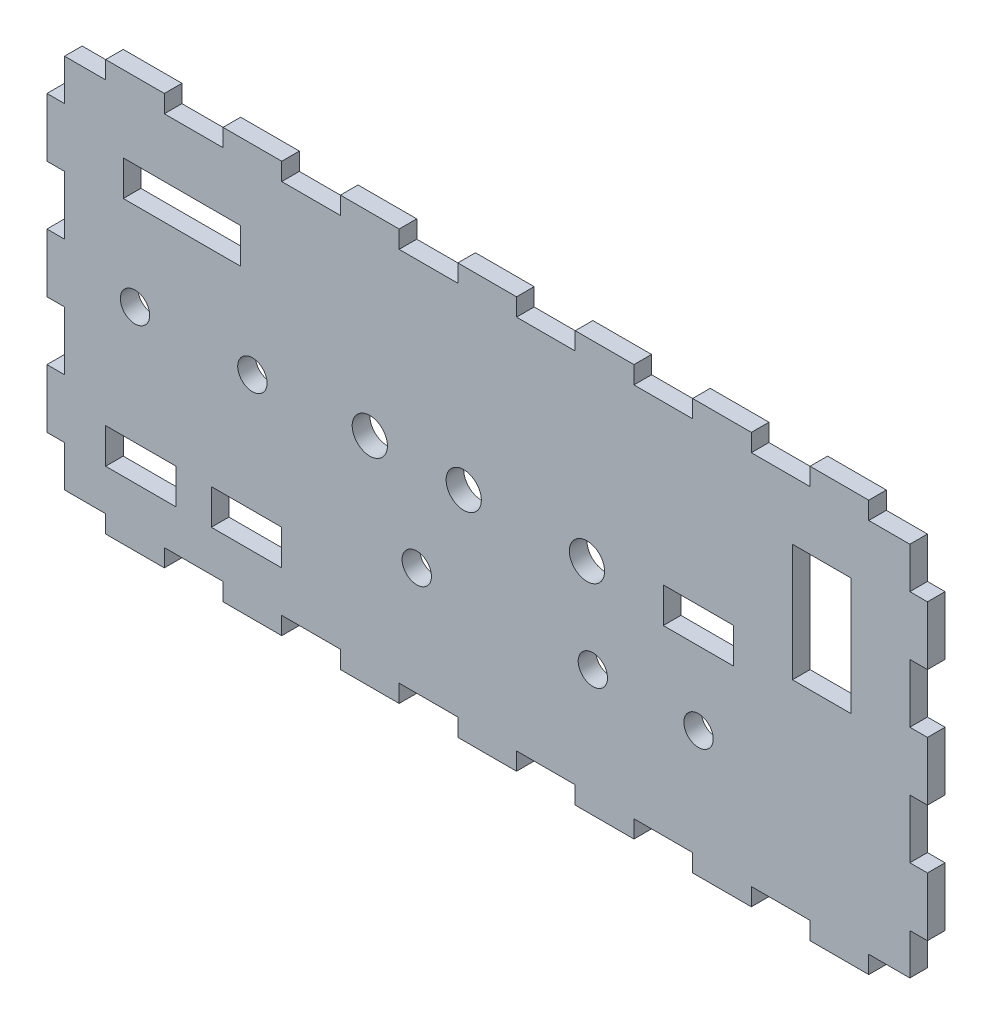
SolidWorks part; units mm, degrees
ref_plane "Front Plane" through (0, 0, 0) normal (0, 0, 1) x (1, 0, 0)
ref_plane "Top Plane" through (0, 0, 0) normal (0, 1, 0) x (1, 0, 0)
ref_plane "Right Plane" through (0, 0, 0) normal (1, 0, 0) x (0, 0, -1)
sketch "Sketch1" plane through (0, 0, 0) normal (0, 0, 1) x (1, 0, 0)
  line L1 (-75, 35) -> (75, 35)
  line L2 (-75, 35) -> (-75, -35)
  line L3 (-75, -35) -> (75, -35)
  line L4 (75, 35) -> (75, -35)
  line L5 (-75, 35) -> (75, -35) construction
  line L6 (-75, -35) -> (75, 35) construction
  point P0 (0, 0)
  dimension "D1" = 150
  dimension "D2" = 70
extrude "Boss-Extrude1" add sketch "Sketch1" along normal blind 3
sketch "Sketch2" plane through (0, 0, 3) normal (0, 0, 1) x (1, 0, 0)
  line L1 (-75, 35) -> (-65, 35)
  line L2 (-75, 35) -> (-75, 32)
  line L3 (-75, 32) -> (-65, 32)
  line L4 (-65, 35) -> (-65, 32)
  dimension "D1" = 3
  dimension "D2" = 10
extrude "Cut-Extrude1" cut sketch "Sketch2" against normal blind 3
pattern_linear "LPattern3" count 8 spacing 20 along (1, 0, 0) of "Cut-Extrude1"
mirror "Mirror1" about plane through (0, 0, 0) normal (0, 1, 0) of "LPattern3", "Cut-Extrude1"
sketch "Sketch3" plane through (0, 0, 3) normal (0, 0, 1) x (1, 0, 0)
  line L0 (-75, 32) -> (-75, -32) construction
  line L1 (-75, 25) -> (-72, 25)
  line L2 (-75, 25) -> (-75, 35)
  line L3 (-75, 35) -> (-72, 35)
  line L4 (-72, 25) -> (-72, 35)
  line L5 (-55, 35) -> (-65, 35) construction
  dimension "D1" = 10
  dimension "D2" = 3
extrude "Cut-Extrude2" cut sketch "Sketch3" against normal blind 3
pattern_linear "LPattern4" count 4 spacing 20 along (0, -1, 0) of "Cut-Extrude2"
mirror "Mirror2" about plane through (0, 0, 0) normal (1, 0, 0) of "LPattern4", "Cut-Extrude2"
sketch "Sketch4" plane through (0, 0, 3) normal (0, 0, 1) x (1, 0, 0)
  line L0 (-55, 35) -> (-65, 35) construction
  line L1 (-62, 22) -> (-42, 22)
  line L2 (-62, 22) -> (-62, 16)
  line L3 (-62, 16) -> (-42, 16)
  line L4 (-42, 22) -> (-42, 16)
  line L5 (-75, 25) -> (-75, 15) construction
  dimension "D1" = 20
  dimension "D2" = 6
  dimension "D3" = 13
  dimension "D4" = 13
extrude "Cut-Extrude3" cut sketch "Sketch4" against normal blind 3
sketch "Sketch5" plane through (0, 0, 3) normal (0, 0, 1) x (1, 0, 0)
  line L0 (-62, 16) -> (-42, 16) construction
  line L1 (-75, 5) -> (-75, -5) construction
  circle A0 centre (-60, 1) radius 2.5
  circle A1 centre (-40, 1) radius 2.5
  dimension "D1" = 5
  dimension "D2" = 5
  dimension "D3" = 15
  dimension "D4" = 15
  dimension "D5" = 15
  dimension "D6" = 20
extrude "Cut-Extrude5" cut sketch "Sketch5" against normal blind 3
sketch "Sketch6" plane through (0, 0, 3) normal (0, 0, 1) x (1, 0, 0)
  line L0 (-65, -35) -> (-55, -35) construction
  line L1 (-65, -19) -> (-53, -19)
  line L2 (-65, -19) -> (-65, -25)
  line L3 (-65, -25) -> (-53, -25)
  line L4 (-53, -19) -> (-53, -25)
  line L5 (-47, -19) -> (-35, -19)
  line L6 (-47, -19) -> (-47, -25)
  line L7 (-47, -25) -> (-35, -25)
  line L8 (-35, -19) -> (-35, -25)
  line L9 (-75, -15) -> (-75, -25) construction
  line L10 (-45, -35) -> (-35, -35) construction
  dimension "D1" = 12
  dimension "D2" = 6
  dimension "D3" = 12
  dimension "D4" = 6
  dimension "D5" = 6
  dimension "D6" = 10
  dimension "D7" = 10
  dimension "D8" = 10
extrude "Cut-Extrude6" cut sketch "Sketch6" against normal blind 3
sketch "Sketch7" plane through (0, 0, 3) normal (0, 0, 1) x (1, 0, 0)
  line L0 (-15, 35) -> (-25, 35) construction
  line L1 (5, 35) -> (-5, 35) construction
  circle A0 centre (-20, 2) radius 3
  circle A1 centre (-4, 2) radius 3
  circle A2 centre (-40, 1) radius 2.5 construction
  dimension "D1" = 6
  dimension "D2" = 6
  dimension "D3" = 20
  dimension "D4" = 16
  dimension "D5" = 33
  dimension "D6" = 33
extrude "Cut-Extrude7" cut sketch "Sketch7" against normal blind 3
sketch "Sketch8" plane through (0, 0, 3) normal (0, 0, 1) x (1, 0, 0)
  line L0 (-75, -15) -> (-75, -25) construction
  circle A0 centre (-12, -13.5) radius 2.5
  circle A1 centre (-20, 2) radius 3 construction
  dimension "D1" = 5
  dimension "D3" = 15.5
  dimension "D2" = 63
extrude "Cut-Extrude8" cut sketch "Sketch8" against normal blind 3
sketch "Sketch9" plane through (0, 0, 3) normal (0, 0, 1) x (1, 0, 0)
  line L0 (25, 35) -> (15, 35) construction
  circle A0 centre (17, 2) radius 3
  circle A1 centre (-4, 2) radius 3 construction
  dimension "D1" = 6
  dimension "D3" = 21
  dimension "D2" = 33
extrude "Cut-Extrude9" cut sketch "Sketch9" against normal blind 3
sketch "Sketch10" plane through (0, 0, 3) normal (0, 0, 1) x (1, 0, 0)
  line L0 (45, 35) -> (35, 35) construction
  line L1 (30, 5) -> (42, 5)
  line L2 (30, 5) -> (30, -1)
  line L3 (30, -1) -> (42, -1)
  line L4 (42, 5) -> (42, -1)
  circle A0 centre (17, 2) radius 3 construction
  dimension "D1" = 6
  dimension "D2" = 12
  dimension "D3" = 30
  dimension "D4" = 13
extrude "Cut-Extrude10" cut sketch "Sketch10" against normal blind 3
sketch "Sketch11" plane through (0, 0, 3) normal (0, 0, 1) x (1, 0, 0)
  line L0 (25, 35) -> (15, 35) construction
  line L1 (45, 35) -> (35, 35) construction
  circle A0 centre (18, -13.5) radius 2.5
  circle A1 centre (36, -13.5) radius 2.5
  circle A2 centre (-12, -13.5) radius 2.5 construction
  dimension "D1" = 5
  dimension "D2" = 5
  dimension "D3" = 48.5
  dimension "D4" = 48.5
  dimension "D5" = 18
  dimension "D6" = 30
extrude "Cut-Extrude11" cut sketch "Sketch11" against normal blind 3
sketch "Sketch12" plane through (0, 0, 3) normal (0, 0, 1) x (1, 0, 0)
  line L0 (65, 35) -> (55, 35) construction
  line L1 (52, 22) -> (62, 22)
  line L2 (52, 22) -> (52, 2)
  line L3 (52, 2) -> (62, 2)
  line L4 (62, 22) -> (62, 2)
  line L5 (65, 35) -> (55, 35) construction
  line L6 (75, 15) -> (75, 25) construction
  point P4 (60, 35)
  dimension "D1" = 10
  dimension "D2" = 20
  dimension "D3" = 13
  dimension "D4" = 13
extrude "Cut-Extrude12" cut sketch "Sketch12" against normal blind 3
